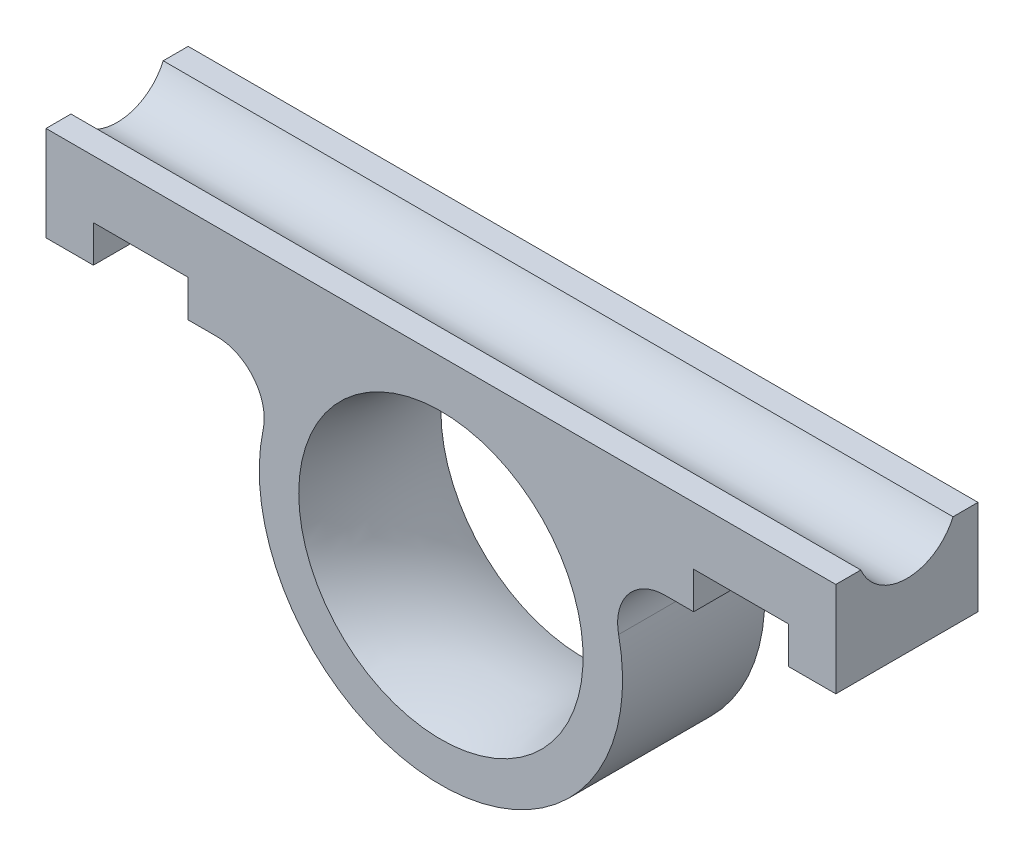
SolidWorks part; units mm, degrees
ref_plane "Front Plane" through (0, 0, 0) normal (0, 0, 1) x (1, 0, 0)
ref_plane "Top Plane" through (0, 0, 0) normal (0, 1, 0) x (1, 0, 0)
ref_plane "Right Plane" through (0, 0, 0) normal (1, 0, 0) x (0, 0, -1)
sketch "Sketch2" plane through (0, 0, 0) normal (0, 0, 1) x (1, 0, 0)
  line L0 (-25, 8.825) -> (25, 8.825) construction
  line L1 (-25, 12) -> (25, 12)
  line L2 (-25, 12) -> (-25, 6)
  line L3 (-25, 6) -> (-22, 6)
  line L4 (25, 12) -> (25, 6)
  line L5 (-22, 6) -> (-22, 7)
  line L6 (-22, 7) -> (-16, 7)
  line L7 (-16, 7) -> (-16, 6)
  line L8 (16, 6) -> (16, 7)
  line L9 (16, 7) -> (22, 7)
  line L10 (22, 7) -> (22, 6)
  line L11 (-16, 6) -> (-14.1863, 6)
  line L12 (22, 6) -> (25, 6)
  line L13 (14.1863, 6) -> (16, 6)
  line L14 (0, 12) -> (0, 0) construction
  circle A0 centre (0, 0) radius 8.25
  arc A1 (-11.2512, 2.3793) -> (11.2512, 2.3793) centre (0, 0) ccw
  arc A2 (14.1863, 6) -> (11.2512, 2.3793) centre (14.1863, 3) ccw
  arc A3 (-11.2512, 2.3793) -> (-14.1863, 6) centre (-14.1863, 3) ccw
  dimension "D1" = 16.5
  dimension "D2" = 23
  dimension "D10" = 3
  dimension "D3" = 3.175
  dimension "D4" = 12
  dimension "D5" = 6
  dimension "D6" = 1
  dimension "D7" = 3
  dimension "D8" = 6
  dimension "D9" = 50
extrude "Boss-Extrude1" add sketch "Sketch2" along normal blind 9
sketch "Sketch3" plane through (25, 0, 0) normal (1, 0, 0) x (0, 0, -1)
  line L1 (-4.5, 13.25) -> (-4.5, 12) construction
  line L2 (-9, 12) -> (0, 12) construction
  circle A0 centre (-4.5, 13.25) radius 3.175
  dimension "D1" = 6.35
  dimension "D2" = 1.25
extrude "Cut-Extrude1" cut sketch "Sketch3" against normal through all
sketch "Sketch4" plane through (-22, 0, 0) normal (1, 0, 0) x (0, 0, -1)
  line L0 (-9, 7) -> (0, 7) construction
  line L1 (-4.5, 15.25) -> (-4.5, 13.25) construction
  circle A0 centre (-4.5, 15.25) radius 8.25
  dimension "D1" = 2
extrude "Cut-Extrude2" cut sketch "Sketch4" along normal up to surface (6 mm away) flip side to cut up to face at (-16, 6.5, 4.5)
sketch "Sketch5" plane through (16, 0, 0) normal (-1, 0, 0) x (0, 0, 1)
  line L3 (0, 8.3353) -> (0, 6)
  line L4 (0, 6) -> (9, 6)
  line L5 (9, 6) -> (9, 8.3353)
  line L6 (0, 8.3353) -> (0, 6)
  line L7 (0, 6) -> (9, 6)
  line L8 (9, 6) -> (9, 8.3353)
  arc A1 (0, 8.3353) -> (9, 8.3353) centre (4.5, 15.25) ccw
  arc A2 (0, 8.3353) -> (9, 8.3353) centre (4.5, 15.25) ccw
  dimension "D1" = 0
extrude "Cut-Extrude3" cut sketch "Sketch5" against normal up to surface (6 mm away) up to face at (22, 6.5, 4.5)
sketch "Sketch6" plane through (0, 0, 0) normal (1, 0, 0) x (0, 0, -1)
  line L0 (-9, 8.25) -> (-9, -8.25) construction
  line L1 (-9, 8.25) -> (-9, -8.25) construction
  line L2 (0, -8.25) -> (0, 8.25) construction
  line L3 (0, -8.25) -> (0, 8.25) construction
  line L4 (-9, 8.25) -> (0, 8.25) construction
  line L5 (-4.5, 22.125) -> (-4.5, 13.25) construction
  line L6 (-9, 9) -> (-9, 0)
  line L7 (-9, 0) -> (0, 0)
  line L8 (0, 0) -> (0, 9)
  line L9 (0, 6) -> (0, 12) construction
  line L10 (-9, 6) -> (-9, 12) construction
  line L11 (-9, 0) -> (-19.7115, 0) construction
  arc A0 (-9, 9) -> (0, 9) centre (-4.5, 22.125) ccw
  dimension "D1" = 9
revolve "Cut-Revolve1" cut sketch "Sketch6" angle 360 about L11
